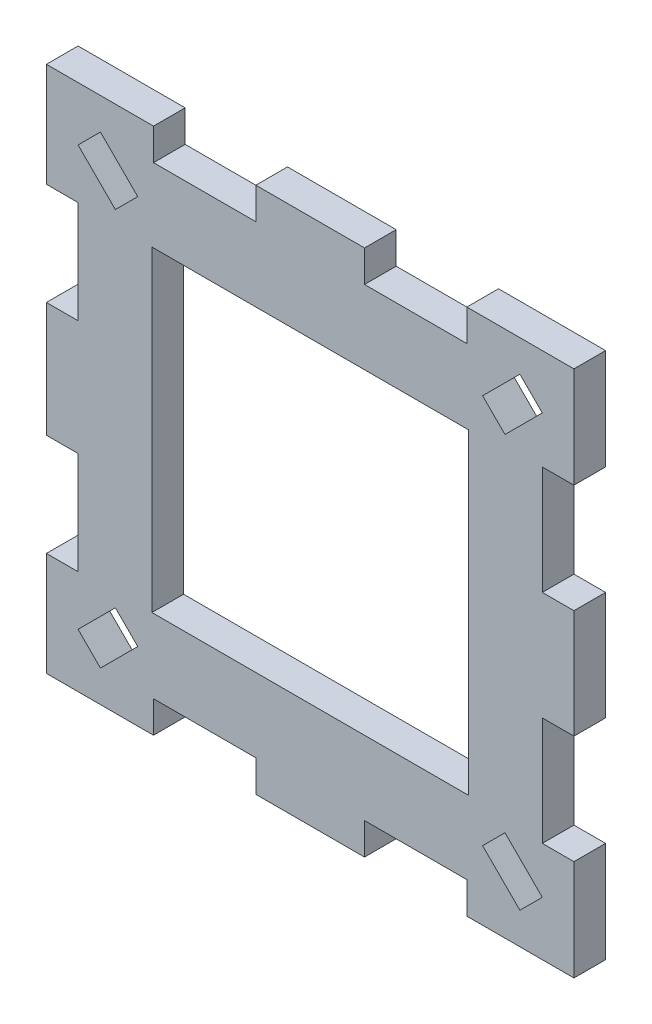
SolidWorks part; units mm, degrees
ref_plane "Alzado" through (0, 0, 0) normal (0, 0, 1) x (1, 0, 0)
ref_plane "Planta" through (0, 0, 0) normal (0, 1, 0) x (1, 0, 0)
ref_plane "Vista lateral" through (0, 0, 0) normal (1, 0, 0) x (0, 0, -1)
sketch "Croquis1" plane through (0, 0, 0) normal (0, 0, 1) x (1, 0, 0)
  line L0 (0, 20.8752) -> (0, -20.0871) construction
  line L1 (-25, -25) -> (-14.85, -25)
  line L2 (-25, -25) -> (-25, -15.15)
  line L3 (-25, 25) -> (-14.85, 25)
  line L4 (25, -25) -> (25, -15.45)
  line L5 (-25, -25) -> (25, 25) construction
  line L6 (-25, 25) -> (25, -25) construction
  line L7 (-23.5, 0) -> (26.5, 0) construction
  line L8 (25, 15.45) -> (22, 15.45)
  line L10 (25, 5.15) -> (22, 5.15)
  line L11 (22, 15.45) -> (22, 5.15)
  line L16 (25, -15.45) -> (22, -15.45)
  line L17 (22, -15.45) -> (22, -5.15)
  line L18 (25, -5.15) -> (22, -5.15)
  line L19 (25, -5.15) -> (25, 5.15)
  line L20 (25, 15.45) -> (25, 25)
  line L21 (22, 5.15) -> (22, 10.3) construction
  line L22 (-25, 15.15) -> (-22, 15.15)
  line L24 (-25, 5.45) -> (-22, 5.45)
  line L25 (-22, 15.15) -> (-22, 5.45)
  line L26 (-22, 5.45) -> (-22, 10.3) construction
  line L27 (22, 10.3) -> (-22, 10.3) construction
  line L28 (-25, 15.15) -> (-25, 25)
  line L29 (-25, -5.45) -> (-22, -5.45)
  line L30 (-22, -15.15) -> (-22, -5.45)
  line L31 (-25, -15.15) -> (-22, -15.15)
  line L32 (-25, -5.45) -> (-25, 5.45)
  line L33 (-5.15, -25) -> (5.15, -25)
  line L35 (-14.85, -25) -> (-14.85, -22)
  line L36 (-14.85, -22) -> (-5.15, -22)
  line L37 (-5.15, -25) -> (-5.15, -22)
  line L38 (5.15, -25) -> (5.15, -22)
  line L39 (14.85, -22) -> (5.15, -22)
  line L40 (14.85, -25) -> (14.85, -22)
  line L41 (14.85, -25) -> (25, -25)
  line L42 (14.85, 25) -> (14.85, 22)
  line L43 (14.85, 22) -> (5.15, 22)
  line L44 (5.15, 25) -> (5.15, 22)
  line L45 (-5.15, 25) -> (-5.15, 22)
  line L46 (-14.85, 22) -> (-5.15, 22)
  line L47 (-14.85, 25) -> (-14.85, 22)
  line L48 (-5.15, 25) -> (5.15, 25)
  line L49 (14.85, 25) -> (25, 25)
  point P0 (0, 0)
  point P46 (25, 0)
  dimension "D5" = 9.7
  dimension "D6" = 3
  dimension "D7" = 3
  dimension "D8" = 9.7
  dimension "D9" = 5.15
  dimension "D3" = 3
  dimension "D2" = 50
  dimension "D10" = 50
  dimension "D4" = 5.15
extrude "Saliente-Extruir1" add sketch "Croquis1" along normal blind 3
sketch "Croquis2" plane through (0, 0, 3) normal (0, 0, 1) x (1, 0, 0)
  line L1 (-15, -15) -> (15, -15)
  line L2 (-15, -15) -> (-15, 15)
  line L3 (-15, 15) -> (15, 15)
  line L4 (15, -15) -> (15, 15)
  line L5 (-15, -15) -> (15, 15) construction
  line L6 (-15, 15) -> (15, -15) construction
  line L7 (-25, 5.45) -> (-25, -5.45) construction
  line L8 (-5.15, -25) -> (5.15, -25) construction
  line L9 (25, -5.15) -> (25, 5.15) construction
  point P0 (0, 0)
  dimension "D1" = 30
  dimension "D3" = 10
  dimension "D4" = 10
  dimension "D2" = 10
extrude "Cortar-Extruir2" cut sketch "Croquis2" against normal blind 3
sketch "Croquis3" plane through (0, 0, 3) normal (0, 0, 1) x (1, 0, 0)
  line L0 (-19.8787, -22) -> (-16.3431, -18.4645)
  line L1 (-19.8787, -22) -> (-22, -19.8787)
  line L2 (-16.3431, -18.4645) -> (-18.4645, -16.3431)
  line L3 (-22, -19.8787) -> (-18.4645, -16.3431)
  line L4 (-14.85, -22) -> (-5.15, -22) construction
  line L5 (-25, -25) -> (-14.85, -25) construction
  line L6 (-25, -15.15) -> (-25, -25) construction
  line L7 (0, 0) -> (0, -15) construction
  line L8 (-15, -15) -> (15, -15) construction
  line L9 (0, -15) -> (0, 0) construction
  line L10 (0, 0) -> (15, 0) construction
  line L11 (15, -15) -> (15, 15) construction
  line L12 (16.3431, -18.4645) -> (18.4645, -16.3431)
  line L13 (19.8787, -22) -> (22, -19.8787)
  line L14 (19.8787, -22) -> (16.3431, -18.4645)
  line L15 (22, -19.8787) -> (18.4645, -16.3431)
  line L16 (22, 19.8787) -> (18.4645, 16.3431)
  line L17 (19.8787, 22) -> (16.3431, 18.4645)
  line L18 (19.8787, 22) -> (22, 19.8787)
  line L19 (16.3431, 18.4645) -> (18.4645, 16.3431)
  line L20 (-22, 19.8787) -> (-18.4645, 16.3431)
  line L21 (-16.3431, 18.4645) -> (-18.4645, 16.3431)
  line L22 (-19.8787, 22) -> (-22, 19.8787)
  line L23 (-19.8787, 22) -> (-16.3431, 18.4645)
  dimension "D2" = 3
  dimension "D3" = 5
  dimension "D4" = 3
  dimension "D5" = 45
extrude "Cortar-Extruir3" cut sketch "Croquis3" against normal blind 3
equation "\"A\"= 3"
equation "\"B\"= 50"
equation "\"C\"= 10"
equation "\"D\"= 10"
equation "\"D5@Croquis1\"=\"C\"-.3"
equation "\"D6@Croquis1\"=\"A\""
equation "\"D7@Croquis1\"=\"A\""
equation "\"D8@Croquis1\"=\"C\"-.3"
equation "\"D9@Croquis1\"=(\"D\"+.3)/2"
equation "\"D1@Croquis2\"=\"C\"*3"
equation "\"D3@Croquis2\"=\"C\""
equation "\"D4@Croquis2\"=\"C\""
equation "\"D2@Croquis3\"=\"A\""
equation "\"D3@Croquis3\"=\"C\"/2"
equation "\"D1@Croquis3\"=\"A\""
equation "\"D3@Croquis1\"=\"A\""
equation "\"D2@Croquis1\"=\"B\""
equation "\"D10@Croquis1\"=\"B\""
equation "\"D4@Croquis1\"=(\"D\"+.3)/2"
equation "\"D2@Croquis2\"=\"C\""
